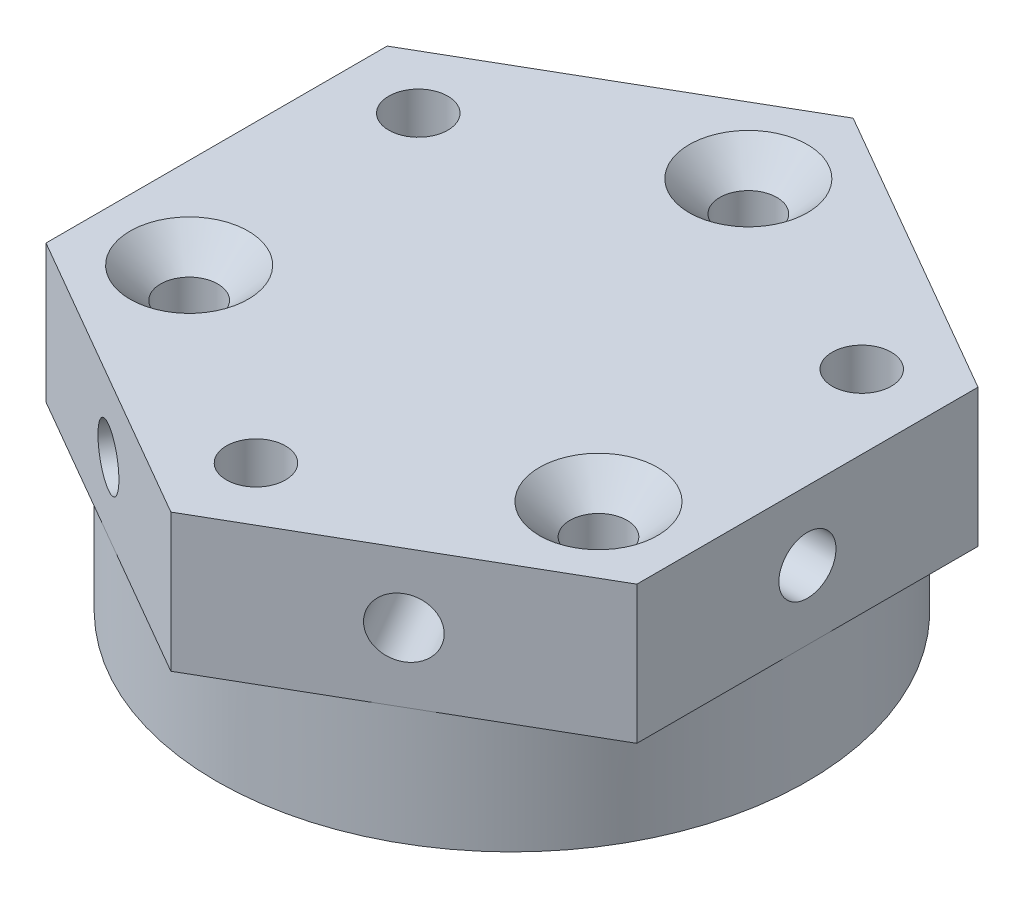
SolidWorks part; units mm, degrees
material "6061 合金"
ref_plane "前视基准面" through (0, 0, 0) normal (0, 0, 1) x (1, 0, 0)
ref_plane "上视基准面" through (0, 0, 0) normal (0, 1, 0) x (1, 0, 0)
ref_plane "右视基准面" through (0, 0, 0) normal (1, 0, 0) x (0, 0, -1)
sketch "草图1" plane through (0, 0, 0) normal (0, 1, 0) x (1, 0, 0)
  line L0 (0, 0) -> (0, 33.3478) construction
  line L1 (0, 0) -> (11.2563, 0) construction
  line L2 (-10.3923, -6) -> (0, 0) construction
  line L3 (0, 0) -> (10.3923, -6) construction
  line L4 (0, 0) -> (-11.2583, 6.5) construction
  line L5 (11.2583, 6.5) -> (0, 0) construction
  circle A0 centre (0, 0) radius 15
  circle A1 centre (0, 12) radius 1.45
  circle A2 centre (0, 0) radius 12 construction
  circle A3 centre (-10.3923, -6) radius 1.45
  circle A4 centre (10.3923, -6) radius 1.45
  circle A5 centre (0, 0) radius 13 construction
  circle A6 centre (-11.2583, 6.5) radius 1.5
  circle A7 centre (0, -13) radius 1.5
  circle A8 centre (11.2583, 6.5) radius 1.5
  dimension "D1" = 30
  dimension "D2" = 24
  dimension "D3" = 2.9
  dimension "D6" = 26
  dimension "D8" = 3
  dimension "D4" = 120
  dimension "D5" = 120
  dimension "D7" = 60
  dimension "D9" = 60
extrude "凸台-拉伸1" add sketch "草图1" along normal blind 13
sketch "草图2" plane through (0, 13, 0) normal (0, 1, 0) x (1, 0, 0)
  line L0 (0, 17.3205) -> (0, 0) construction
  line L1 (0, 17.3205) -> (-15, 8.6603)
  line L2 (-15, 8.6603) -> (-15, -8.6603)
  line L3 (-15, -8.6603) -> (0, -17.3205)
  line L4 (0, -17.3205) -> (15, -8.6603)
  line L5 (15, -8.6603) -> (15, 8.6603)
  line L6 (15, 8.6603) -> (0, 17.3205)
  circle A0 centre (0, 0) radius 15 construction
  circle A1 centre (0, 12) radius 1.45
  circle A2 centre (0, 12) radius 1.45 construction
  circle A3 centre (-11.2583, 6.5) radius 1.5
  circle A4 centre (-11.2583, 6.5) radius 1.5 construction
  circle A5 centre (11.2583, 6.5) radius 1.5
  circle A6 centre (11.2583, 6.5) radius 1.5 construction
  circle A7 centre (-10.3923, -6) radius 1.45
  circle A8 centre (-10.3923, -6) radius 1.45 construction
  circle A9 centre (0, -13) radius 1.5
  circle A10 centre (0, -13) radius 1.5 construction
  circle A11 centre (10.3923, -6) radius 1.45
  circle A12 centre (10.3923, -6) radius 1.45 construction
  dimension "D1" = 30
extrude "凸台-拉伸2" add sketch "草图2" against normal blind 7
sketch "草图3" plane through (7.5, 0, 12.9904) normal (0.5, 0, 0.866) x (0.866, 0, -0.5)
  line L1 (0, 13) -> (0, 6) construction
  line L2 (-8.6603, 13) -> (8.6603, 13) construction
  circle A1 centre (0, 9.5) radius 1.45
  dimension "D1" = 2.9
extrude "切除-拉伸1" cut sketch "草图3" against normal through all
sketch "草图4" plane through (-7.5, 0, 12.9904) normal (-0.5, 0, 0.866) x (0.866, 0, 0.5)
  line L0 (0, 6) -> (0, 13) construction
  line L1 (-8.6603, 13) -> (8.6603, 13) construction
  circle A0 centre (0, 9.5) radius 1.45
  dimension "D1" = 2.9
extrude "切除-拉伸2" cut sketch "草图4" against normal through all
sketch "草图5" plane through (-15, 0, 0) normal (-1, 0, 0) x (0, 0, 1)
  line L0 (0, 6) -> (0, 13) construction
  line L1 (-8.6603, 13) -> (8.6603, 13) construction
  circle A0 centre (0, 9.5) radius 1.45
  dimension "D1" = 2.9
extrude "切除-拉伸3" cut sketch "草图5" against normal through all
sketch "草图8" plane through (-7.5, 0, -12.9904) normal (-0.5, 0, -0.866) x (-0.866, 0, 0.5)
  line L0 (0, 13) -> (0, 9.5) construction
  line L1 (-8.6603, 13) -> (8.6603, 13) construction
  circle A0 centre (0, 9.5) radius 1.5
  dimension "D1" = 3
  dimension "D2" = 3.5
extrude "切除-拉伸6" cut sketch "草图8" against normal through all
chamfer "倒角1" distance 1.55 angle 45 3 edges at (-10.3923, 13, 7.45) (0, 13, -10.55) (10.3923, 13, 7.45)
